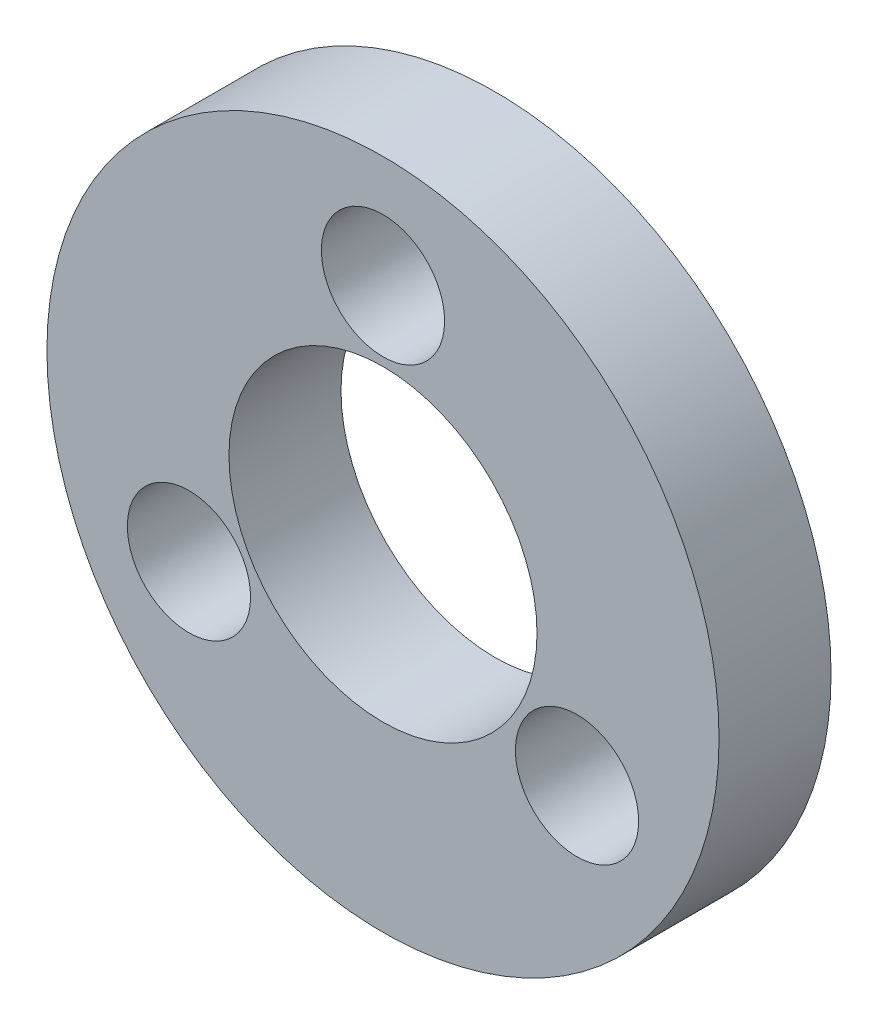
SolidWorks part; units mm, degrees
ref_plane "Front Plane" through (0, 0, 0) normal (0, 0, 1) x (1, 0, 0)
ref_plane "Top Plane" through (0, 0, 0) normal (0, 1, 0) x (1, 0, 0)
ref_plane "Right Plane" through (0, 0, 0) normal (1, 0, 0) x (0, 0, -1)
sketch "Sketch1" plane through (0, 0, 0) normal (0, 0, 1) x (1, 0, 0)
  circle A0 centre (-27.5, 59.9979) radius 6 construction
  circle A1 centre (-27.5, 59.9979) radius 6
  circle A2 centre (-27.5, 59.9979) radius 2.75 construction
  circle A3 centre (-27.5, 59.9979) radius 2.75
extrude "Boss-Extrude1" add sketch "Sketch1" against normal up to vertex (2 mm away)
hole_wizard "M2 Clearance Hole1" positions "Sketch2" profile "Sketch3" hole size "M2" standard "ANSI Metric" end condition through all
sketch "Sketch2" plane through (0, 0, 0) normal (0, 0, 1) x (1, 0, 0)
  point P0 (-27.5, 63.9979)
  point P3 (-24.0359, 57.9979)
  point P6 (-30.9641, 57.9979)
sketch "Sketch3" plane through (-27.5, 63.9979, 0) normal (1, 0, 0) x (0, -1, 0)
  line L0 (0, 0) -> (0, 2)
  line L1 (0, 2) -> (1.1, 2)
  line L2 (1.1, 2) -> (1.1, 0)
  line L5 (1.1, 0) -> (0, 0)
  line L11 (0, -6.35) -> (0, 107.95) construction
  dimension "Thru Hole Dia." = 2.2
  dimension "Thru Hole Depth" = 2
